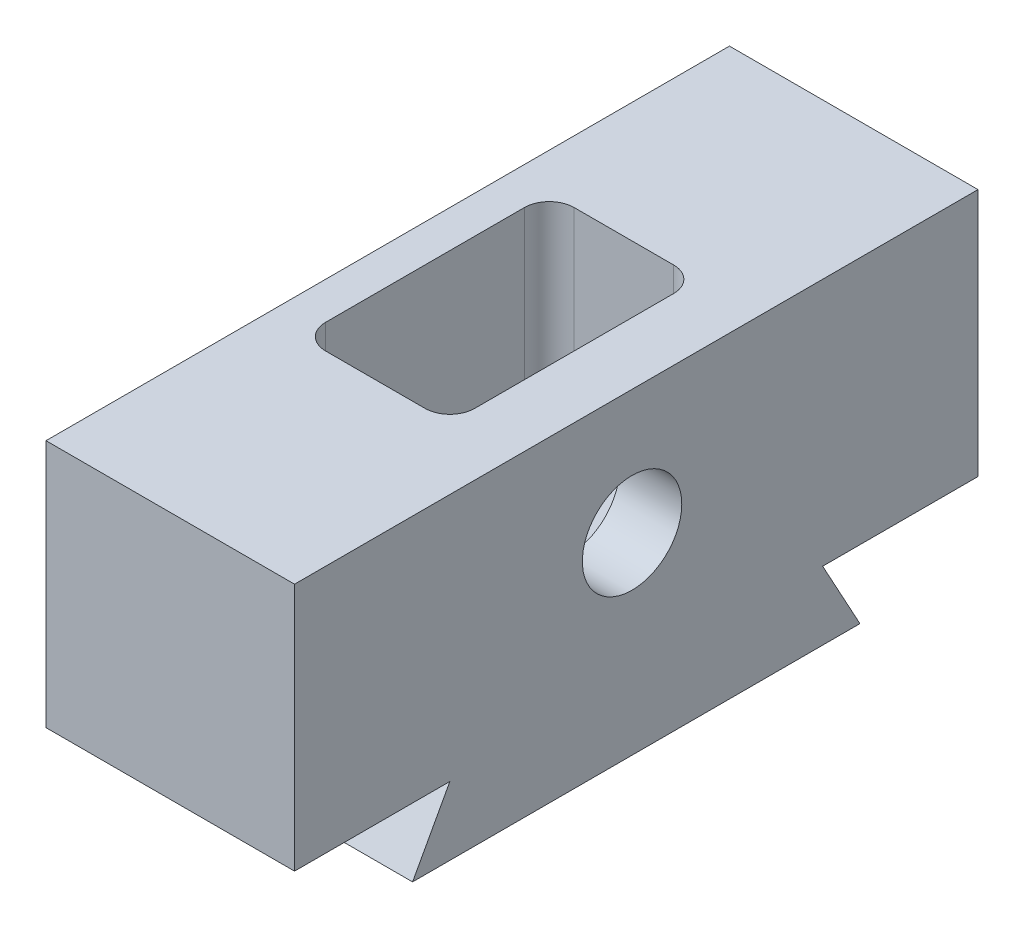
SolidWorks part; units mm, degrees
material "Plain Carbon Steel"
ref_plane "Front Plane" through (0, 0, 0) normal (0, 0, 1) x (1, 0, 0)
ref_plane "Top Plane" through (0, 0, 0) normal (0, 1, 0) x (1, 0, 0)
ref_plane "Right Plane" through (0, 0, 0) normal (1, 0, 0) x (0, 0, -1)
sketch "Sketch1" plane through (0, 0, 0) normal (1, 0, 0) x (0, 0, -1)
  line L0 (-55, -20) -> (-42.5, -20)
  line L1 (0, 0) -> (-55, 0)
  line L2 (0, 0) -> (0, -20)
  line L4 (-55, 0) -> (-55, -20)
  line L5 (-45.5, -25.5) -> (-9.5, -25.5)
  line L6 (-45.5, -25.5) -> (-42.5, -20)
  line L7 (-9.5, -25.5) -> (-12.5, -20)
  line L8 (-12.5, -20) -> (0, -20)
  point P5 (-45.5, -25.5)
  point P6 (-9.5, -25.5)
  point P7 (-12.5, -20)
  point P10 (-42.5, -20)
  dimension "D1" = 5.5
  dimension "D2" = 55
  dimension "D3" = 20
  dimension "D4" = 12.5
  dimension "D5" = 12.5
  dimension "D6" = 36
  dimension "D7" = 3
extrude "Boss-Extrude1" add sketch "Sketch1" along normal mid plane 20
hole_wizard "Ø8.0mm Dowel Hole2" positions "3DSketch2" profile "Sketch3" hole size "Ø8.0" standard "ANSI Metric"
sketch3d "3DSketch2"
  line L0 (10, 0, 55) -> (10, -20, 55) construction
  line L1 (10, -25.5, 45.5) -> (10, -25.5, 9.5) construction
  point P0 (10, -10, 27.8389)
  dimension "D1" = 27.1611
  dimension "D2" = 15.5
sketch "Sketch3" plane through (10, -10, 27.8389) normal (0, 1, 0) x (0, 0, -1)
  line L0 (0, 0) -> (0, 5)
  line L1 (0, 5) -> (4, 5)
  line L2 (4, 5) -> (4, 0)
  line L5 (4, 0) -> (0, 0)
  line L10 (0, 5) -> (-4, 5) construction
  line L11 (0, -6.35) -> (0, 107.95) construction
  dimension "Hole Dia." = 8
  dimension "Hole Depth" = 5
  dimension "Drill Angle" = 180
hole_wizard "Tap Drill for M5x0.8 Tap1" positions "3DSketch5" profile "Sketch6" hole size "M5x0.8" standard "ANSI Metric"
sketch3d "3DSketch5"
  line L0 (-10, -25.5, 45.5) -> (-10, -25.5, 9.5) construction
  line L1 (-10, -20, 0) -> (-10, 0, 0) construction
  point P0 (-10, -9, 10)
  point P2 (-10, -9, 45)
  dimension "D1" = 16.5
  dimension "D2" = 16.5
  dimension "D3" = 10
  dimension "D4" = 45
sketch "Sketch6" plane through (-10, -9, 10) normal (0, 1, 0) x (0, 0, 1)
  line L0 (0, 0) -> (0, 11.2618)
  line L1 (0, 11.2618) -> (2.1, 10)
  line L2 (2.1, 10) -> (2.1, 0)
  line L5 (2.1, 0) -> (0, 0)
  line L10 (0, 11.2618) -> (-2.1, 10) construction
  line L11 (0, -6.35) -> (0, 107.95) construction
  dimension "Hole Dia." = 4.2
  dimension "Hole Depth" = 10
  dimension "Drill Angle" = 118
sketch "Sketch7" plane through (0, 0, 0) normal (0, 1, 0) x (1, 0, 0)
  line L1 (3, -17.5) -> (-5, -17.5)
  line L2 (5, -19.5) -> (5, -35.5)
  line L3 (3, -37.5) -> (-5, -37.5)
  line L4 (-10, 0) -> (-10, -55)
  line L5 (-10, -55) -> (10, -55)
  line L6 (10, -55) -> (10, 0)
  line L7 (10, 0) -> (-10, 0)
  line L8 (-10, 0) -> (-10, -55)
  line L9 (-10, -55) -> (10, -55)
  line L10 (10, -55) -> (10, 0)
  line L11 (10, 0) -> (-10, 0)
  line L12 (-7, -19.5) -> (-7, -35.5)
  arc A0 (-5, -37.5) -> (-7, -35.5) centre (-5, -35.5) cw
  arc A1 (5, -35.5) -> (3, -37.5) centre (3, -35.5) cw
  arc A2 (3, -17.5) -> (5, -19.5) centre (3, -19.5) cw
  arc A3 (-5, -17.5) -> (-7, -19.5) centre (-5, -19.5) ccw
  point P2 (-10, -37.5)
  point P4 (-10, -17.5)
  point P6 (5, 0)
  point P16 (-7, -37.5)
  point P19 (5, -37.5)
  point P22 (5, -17.5)
  point P25 (-7, -17.5)
  dimension "D6" = 2
  dimension "D2" = 17.5
  dimension "D3" = 20
  dimension "D4" = 5
  dimension "D5" = 12
  dimension "D1" = 0
extrude "Cut-Extrude1" cut sketch "Sketch7" against normal blind 16 flip side to cut
